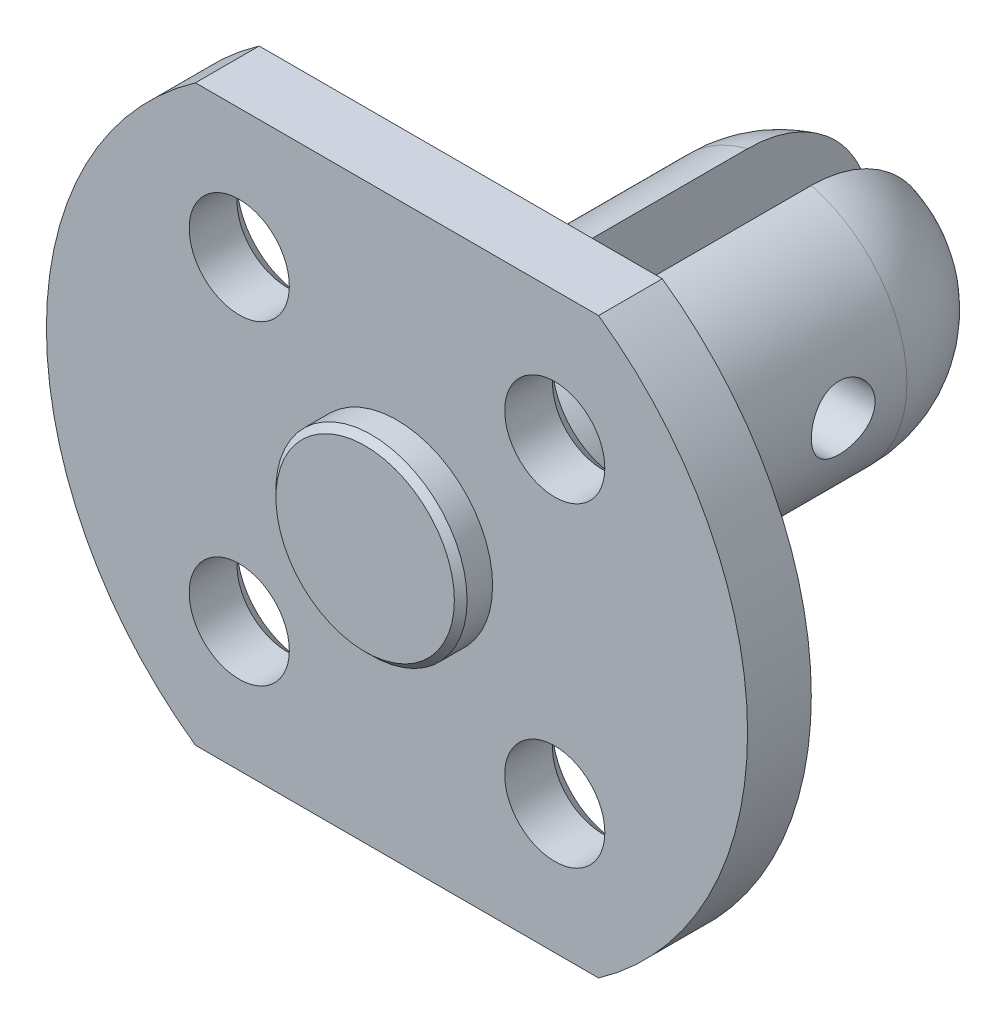
SolidWorks part; units mm, degrees
material "Stainless Steel (ferritic)"
ref_plane "Front Plane" through (0, 0, 0) normal (0, 0, 1) x (1, 0, 0)
ref_plane "Top Plane" through (0, 0, 0) normal (0, 1, 0) x (1, 0, 0)
ref_plane "Right Plane" through (0, 0, 0) normal (1, 0, 0) x (0, 0, -1)
sketch "Sketch1" plane through (0, 0, 0) normal (0, 0, 1) x (1, 0, 0)
  line L7 (-6.3246, 9) -> (6.3246, 9)
  line L9 (-6.3246, -9) -> (6.3246, -9)
  arc A4 (-6.3246, 9) -> (-6.3246, -9) centre (0, 0) ccw
  arc A6 (6.3246, -9) -> (6.3246, 9) centre (0, 0) ccw
extrude "Boss-Extrude1" add sketch "Sketch1" along normal blind 2
sketch "Sketch2" plane through (0, 0, 2) normal (0, 0, 1) x (1, 0, 0)
  circle A0 centre (0, 0) radius 7 construction
  circle A1 centre (4.9497, 4.9497) radius 1.5712
  circle A2 centre (4.9497, -4.9497) radius 1.5712
  circle A3 centre (-4.9497, -4.9497) radius 1.5712
  circle A4 centre (-4.9497, 4.9497) radius 1.5712
  point P16 (0, 0)
  dimension "D1" = 14
  dimension "D3" = 4
extrude "Cut-Extrude1" cut sketch "Sketch2" against normal blind 2
chamfer "Chamfer1" distance 0.5 angle 45 4 edges at (-3.3786, 4.9497, 0) (-3.3786, -4.9497, 0) (6.5209, -4.9497, 0) (6.5209, 4.9497, 0)
sketch "Sketch3" plane through (0, 0, 0) normal (0, 1, 0) x (1, 0, 0)
  line L0 (0, 0) -> (0, 14)
  line L1 (0, 0) -> (4, 0)
  line L2 (9, 0) -> (-9, 0) construction
  line L3 (4, 0) -> (4, 10)
  arc A0 (4, 10) -> (0, 14) centre (0, 10) ccw
  dimension "D1" = 14
  dimension "D2" = 10
  dimension "D3" = 4
revolve "Revolve1" add sketch "Sketch3" angle 360 about L0
sketch "Sketch4" plane through (0, 0, 0) normal (0, 1, 0) x (1, 0, 0)
  line L0 (9, 0) -> (-9, 0) construction
  line L1 (-1, 15.8529) -> (1, 15.8529)
  line L2 (-1, 15.8529) -> (-1, 3.5)
  line L3 (-1, 3.5) -> (1, 3.5)
  line L4 (1, 15.8529) -> (1, 3.5)
  line L5 (-1, 15.8529) -> (1, 3.5) construction
  line L6 (-1, 3.5) -> (1, 15.8529) construction
  point P0 (0, 9.6764)
  dimension "D1" = 3.5
  dimension "D2" = 2
extrude "Cut-Extrude2" cut sketch "Sketch4" against normal mid plane 27
sketch "Sketch5" plane through (0, 0, 0) normal (1, 0, 0) x (0, 0, -1)
  line L0 (0, -5.4083) -> (0, 5.4083) construction
  circle A0 centre (8, 0) radius 1
  dimension "D1" = 2
  dimension "D2" = 8
extrude "Cut-Extrude3" cut sketch "Sketch5" against normal mid plane 27
sketch "Sketch6" plane through (0, 0, 2) normal (0, 0, 1) x (1, 0, 0)
  circle A0 centre (0, 0) radius 3
  dimension "D1" = 6
extrude "Boss-Extrude2" add sketch "Sketch6" along normal blind 1
chamfer "Chamfer2" distance 0.2 angle 45 1 edges at (3, 0, 3)
